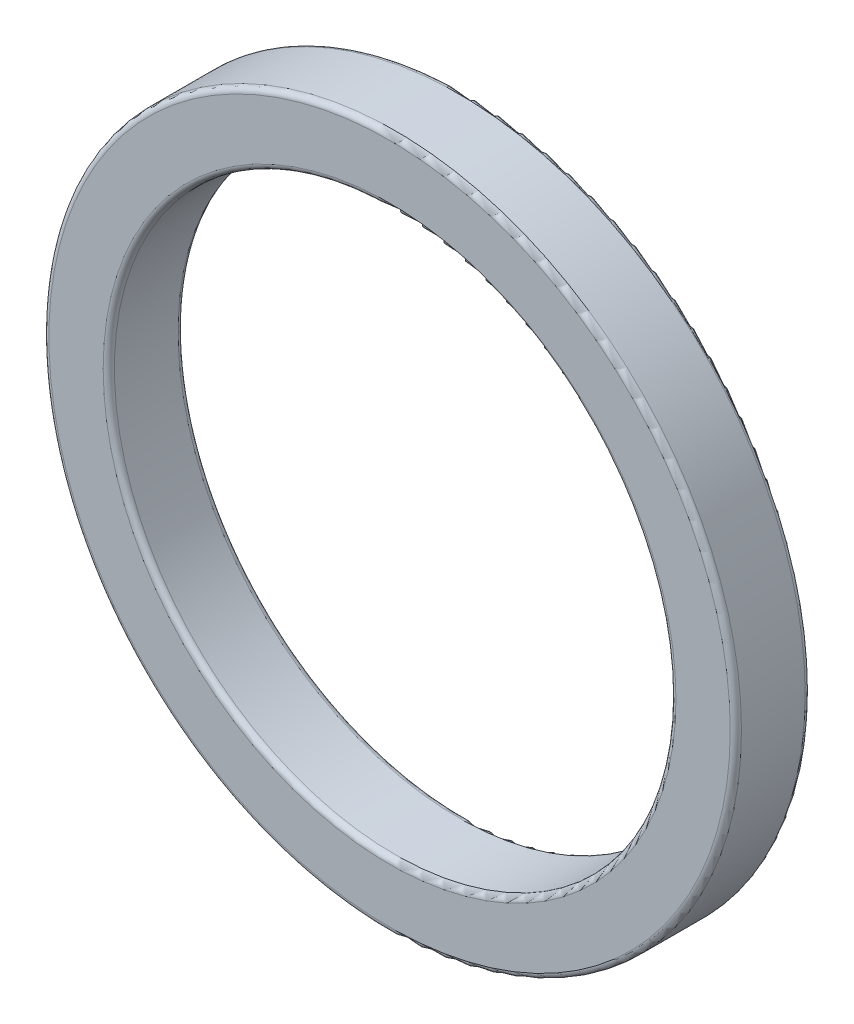
SolidWorks part; units mm, degrees
ref_plane "前视基准面" through (0, 0, 0) normal (0, 0, 1) x (1, 0, 0)
ref_plane "上视基准面" through (0, 0, 0) normal (0, 1, 0) x (1, 0, 0)
ref_plane "右视基准面" through (0, 0, 0) normal (1, 0, 0) x (0, 0, -1)
sketch "草图1" plane through (0, 0, 0) normal (0, 0, 1) x (1, 0, 0)
  circle A0 centre (0, 0) radius 15
  circle A1 centre (0, 0) radius 18.5
  dimension "D1" = 30
  dimension "D2" = 37
extrude "凸台-拉伸1" add sketch "草图1" along normal blind 4
fillet "圆角1" radius 0.3 4 edges at (15, 0, 0) (18.5, 0, 0) (15, 0, 4) (18.5, 0, 4)
